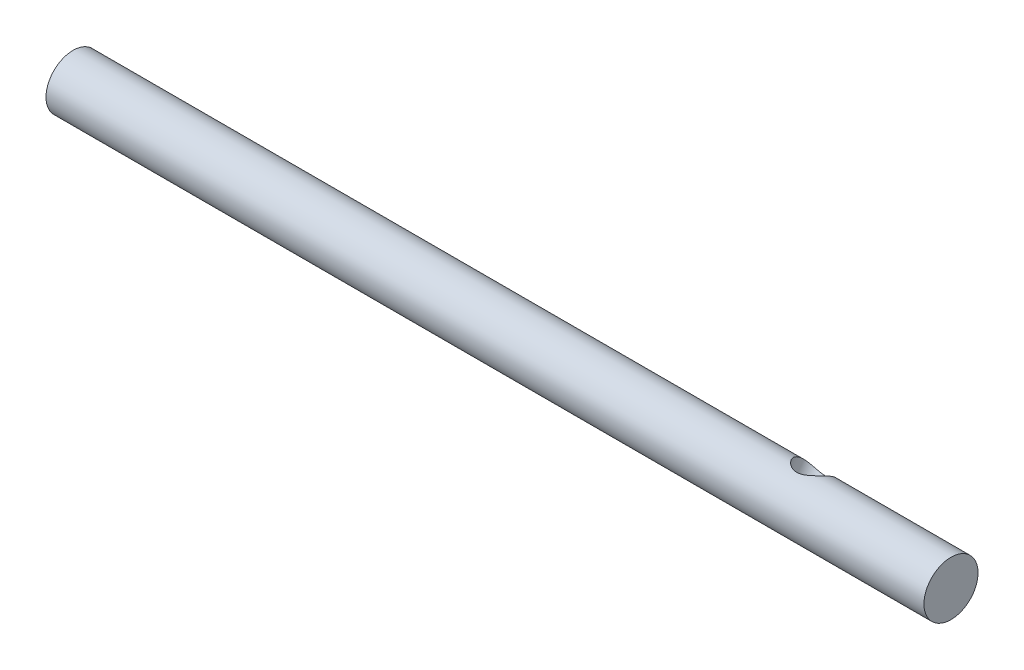
SolidWorks part; units mm, degrees
ref_plane "Front Plane" through (0, 0, 0) normal (0, 0, 1) x (1, 0, 0)
ref_plane "Top Plane" through (0, 0, 0) normal (0, 1, 0) x (1, 0, 0)
ref_plane "Right Plane" through (0, 0, 0) normal (1, 0, 0) x (0, 0, -1)
sketch "Sketch1" plane through (0, 0, 0) normal (1, 0, 0) x (0, 0, -1)
  circle A0 centre (0, 0) radius 4
  dimension "D1" = 8
extrude "Boss-Extrude1" add sketch "Sketch1" along normal mid plane 150
sketch "Sketch2" plane through (-1373.6271, 398.0341, -1457.2495) normal (0, -0.8537, 0.5208) x (0, 0.5208, 0.8537)
  line L0 (1036.7375, -1497.7488) -> (1036.7375, -1368.0826) construction
  line L1 (1032.7375, -1448.6271) -> (1040.7375, -1448.6271) construction
  circle A1 centre (1036.7375, -1406.1271) radius 2.5
  dimension "D1" = 5
  dimension "D2" = 42.5
extrude "Cut-Extrude1" cut sketch "Sketch2" along normal blind 1097
sketch "Sketch3" plane through (0, 0, 0) normal (0, 1, 0) x (1, 0, 0)
  line L1 (95.2, 24.7707) -> (54.8, 24.7707)
  line L2 (95.2, 24.7707) -> (95.2, -16.7707)
  line L3 (95.2, -16.7707) -> (54.8, -16.7707)
  line L4 (54.8, 24.7707) -> (54.8, -16.7707)
  line L5 (95.2, 24.7707) -> (54.8, -16.7707) construction
  line L6 (95.2, -16.7707) -> (54.8, 24.7707) construction
  point P0 (75, 4)
  dimension "D1" = 40.4
extrude "Cut-Extrude2" cut sketch "Sketch3" against normal mid plane 10
